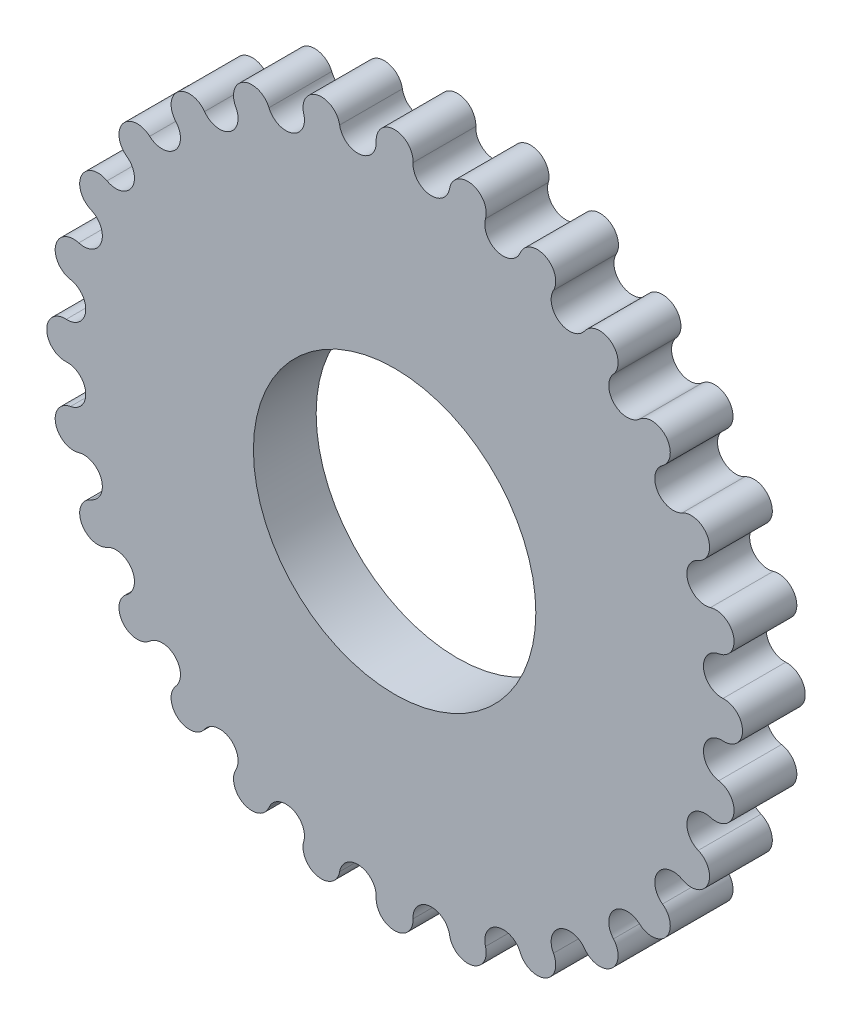
SolidWorks part; units mm, degrees
ref_plane "Front Plane" through (0, 0, 0) normal (0, 0, 1) x (1, 0, 0)
ref_plane "Top Plane" through (0, 0, 0) normal (0, 1, 0) x (1, 0, 0)
ref_plane "Right Plane" through (0, 0, 0) normal (1, 0, 0) x (0, 0, -1)
sketch "Sketch1" plane through (0, 0, 0) normal (0, 0, 1) x (1, 0, 0)
  line L0 (0, 21) -> (0, -21) construction
  circle A0 centre (0, 0) radius 9
  arc A2 (1.1732, 20.9341) -> (-1.1745, 20.9671) centre (0, 21) ccw
  arc A3 (1.1755, 20.9671) -> (3.5099, 20.7046) centre (2.3463, 20.8682) ccw
  arc A4 (5.7924, 20.1504) -> (3.5047, 20.6717) centre (4.6632, 20.4751) ccw
  arc A5 (5.8022, 20.1825) -> (8.02, 19.4082) centre (6.9217, 19.8256) ccw
  arc A6 (10.1223, 18.3605) -> (8.0075, 19.3768) centre (9.0934, 18.9279) ccw
  arc A7 (10.1392, 18.3901) -> (12.1298, 17.1426) centre (11.1513, 17.7931) ccw
  arc A8 (13.9467, 15.6537) -> (12.1103, 17.1143) centre (13.0694, 16.4355) ccw
  arc A9 (13.97, 15.6792) -> (15.6339, 14.0208) centre (14.8239, 14.872) ccw
  arc A10 (17.0744, 12.1653) -> (15.6083, 13.9972) centre (16.3927, 13.1223) ccw
  arc A11 (17.1032, 12.1852) -> (18.3572, 10.1987) centre (17.7562, 11.2083) ccw
  arc A12 (19.3495, 8.0695) -> (18.3267, 10.1812) centre (18.8973, 9.154) ccw
  arc A13 (19.3823, 8.0826) -> (20.1637, 5.8672) centre (19.8017, 6.985) ccw
  arc A14 (20.6582, 3.5707) -> (20.1299, 5.8568) centre (20.4581, 4.7285) ccw
  arc A15 (20.6933, 3.5762) -> (20.9632, 1.2426) centre (20.8583, 2.4129) ccw
  arc A16 (20.9708, -1.1077) -> (20.9278, 1.2399) centre (20.9973, 0.067) ccw
  arc A17 (-20.9708, -1.1077) -> (-20.9278, 1.2399) centre (-20.9973, 0.067) cw
  arc A18 (-20.6933, 3.5762) -> (-20.9632, 1.2426) centre (-20.8583, 2.4129) cw
  arc A19 (-20.6582, 3.5707) -> (-20.1299, 5.8568) centre (-20.4581, 4.7285) cw
  arc A20 (-19.3823, 8.0826) -> (-20.1637, 5.8672) centre (-19.8017, 6.985) cw
  arc A21 (-19.3495, 8.0695) -> (-18.3267, 10.1812) centre (-18.8973, 9.154) cw
  arc A22 (-17.1032, 12.1852) -> (-18.3572, 10.1987) centre (-17.7562, 11.2083) cw
  arc A23 (-17.0744, 12.1653) -> (-15.6083, 13.9972) centre (-16.3927, 13.1223) cw
  arc A24 (-13.97, 15.6792) -> (-15.6339, 14.0208) centre (-14.8239, 14.872) cw
  arc A25 (-13.9467, 15.6537) -> (-12.1103, 17.1143) centre (-13.0694, 16.4355) cw
  arc A26 (-10.1392, 18.3901) -> (-12.1298, 17.1426) centre (-11.1513, 17.7931) cw
  arc A27 (-10.1223, 18.3605) -> (-8.0075, 19.3768) centre (-9.0934, 18.9279) cw
  arc A28 (-5.8022, 20.1825) -> (-8.02, 19.4082) centre (-6.9217, 19.8256) cw
  arc A29 (-5.7924, 20.1504) -> (-3.5047, 20.6717) centre (-4.6632, 20.4751) cw
  arc A30 (-1.1755, 20.9671) -> (-3.5099, 20.7046) centre (-2.3463, 20.8682) cw
  arc A31 (-1.1732, 20.9341) -> (1.1745, 20.9671) centre (0, 21) cw
  arc A32 (-1.1732, -20.8002) -> (1.1745, -20.8332) centre (0, -20.866) ccw
  arc A33 (-1.1755, -20.8331) -> (-3.5099, -20.5707) centre (-2.3463, -20.7343) ccw
  arc A34 (-5.7924, -20.0164) -> (-3.5047, -20.5377) centre (-4.6632, -20.3412) ccw
  arc A35 (-5.8022, -20.0486) -> (-8.02, -19.2743) centre (-6.9217, -19.6917) ccw
  arc A36 (-10.1223, -18.2265) -> (-8.0075, -19.2428) centre (-9.0934, -18.7939) ccw
  arc A37 (-10.1392, -18.2561) -> (-12.1298, -17.0086) centre (-11.1513, -17.6591) ccw
  arc A38 (-13.9467, -15.5198) -> (-12.1103, -16.9803) centre (-13.0694, -16.3015) ccw
  arc A39 (-13.97, -15.5453) -> (-15.6339, -13.8868) centre (-14.8239, -14.7381) ccw
  arc A40 (-17.0744, -12.0314) -> (-15.6083, -13.8632) centre (-16.3927, -12.9884) ccw
  arc A41 (-17.1032, -12.0513) -> (-18.3572, -10.0647) centre (-17.7562, -11.0744) ccw
  arc A42 (-19.3495, -7.9355) -> (-18.3267, -10.0472) centre (-18.8973, -9.02) ccw
  arc A43 (-19.3823, -7.9486) -> (-20.1637, -5.7332) centre (-19.8017, -6.851) ccw
  arc A44 (-20.6582, -3.4367) -> (-20.1299, -5.7228) centre (-20.4581, -4.5946) ccw
  arc A45 (-20.6933, -3.4423) -> (-20.9632, -1.1086) centre (-20.8583, -2.2789) ccw
  arc A46 (-20.9708, 1.2417) -> (-20.9278, -1.106) centre (-20.9973, 0.067) ccw
  arc A47 (20.9708, 1.2417) -> (20.9278, -1.106) centre (20.9973, 0.067) cw
  arc A48 (20.6933, -3.4423) -> (20.9632, -1.1086) centre (20.8583, -2.2789) cw
  arc A49 (20.6582, -3.4367) -> (20.1299, -5.7228) centre (20.4581, -4.5946) cw
  arc A50 (19.3823, -7.9486) -> (20.1637, -5.7332) centre (19.8017, -6.851) cw
  arc A51 (19.3495, -7.9355) -> (18.3267, -10.0472) centre (18.8973, -9.02) cw
  arc A52 (17.1032, -12.0513) -> (18.3572, -10.0647) centre (17.7562, -11.0744) cw
  arc A53 (17.0744, -12.0314) -> (15.6083, -13.8632) centre (16.3927, -12.9884) cw
  arc A54 (13.97, -15.5453) -> (15.6339, -13.8868) centre (14.8239, -14.7381) cw
  arc A55 (13.9467, -15.5198) -> (12.1103, -16.9803) centre (13.0694, -16.3015) cw
  arc A56 (10.1392, -18.2561) -> (12.1298, -17.0086) centre (11.1513, -17.6591) cw
  arc A57 (10.1223, -18.2265) -> (8.0075, -19.2428) centre (9.0934, -18.7939) cw
  arc A58 (5.8022, -20.0486) -> (8.02, -19.2743) centre (6.9217, -19.6917) cw
  arc A59 (5.7924, -20.0164) -> (3.5047, -20.5377) centre (4.6632, -20.3412) cw
  arc A60 (1.1755, -20.8331) -> (3.5099, -20.5707) centre (2.3463, -20.7343) cw
  arc A61 (1.1732, -20.8002) -> (-1.1745, -20.8332) centre (0, -20.866) cw
  point P37 (-0.0025, 0.0001)
  dimension "D1" = 15
  dimension "D2" = 2.35
  dimension "D3" = 18
extrude "Boss-Extrude1" add sketch "Sketch1" along normal blind 4 contours A61 A60 A59 A58 A57 A56 A55 A54 A53 A52 A51 A50 A49 A48 A47 A16 A15 A14 A13 A12 A11 A10 A9 A8 A7 A6 A5 A4 A3 A2 A31 A30 A29 A28 A27 A26 A25 A24 A23 A22 A21 A20 A19 A18 A17 A46 A45 A44
sketch "Sketch2" plane through (0, 0, 4) normal (0, 0, 1) x (1, 0, 0)
  circle A0 centre (0, 14) radius 3 construction
  dimension "D1" = 14
